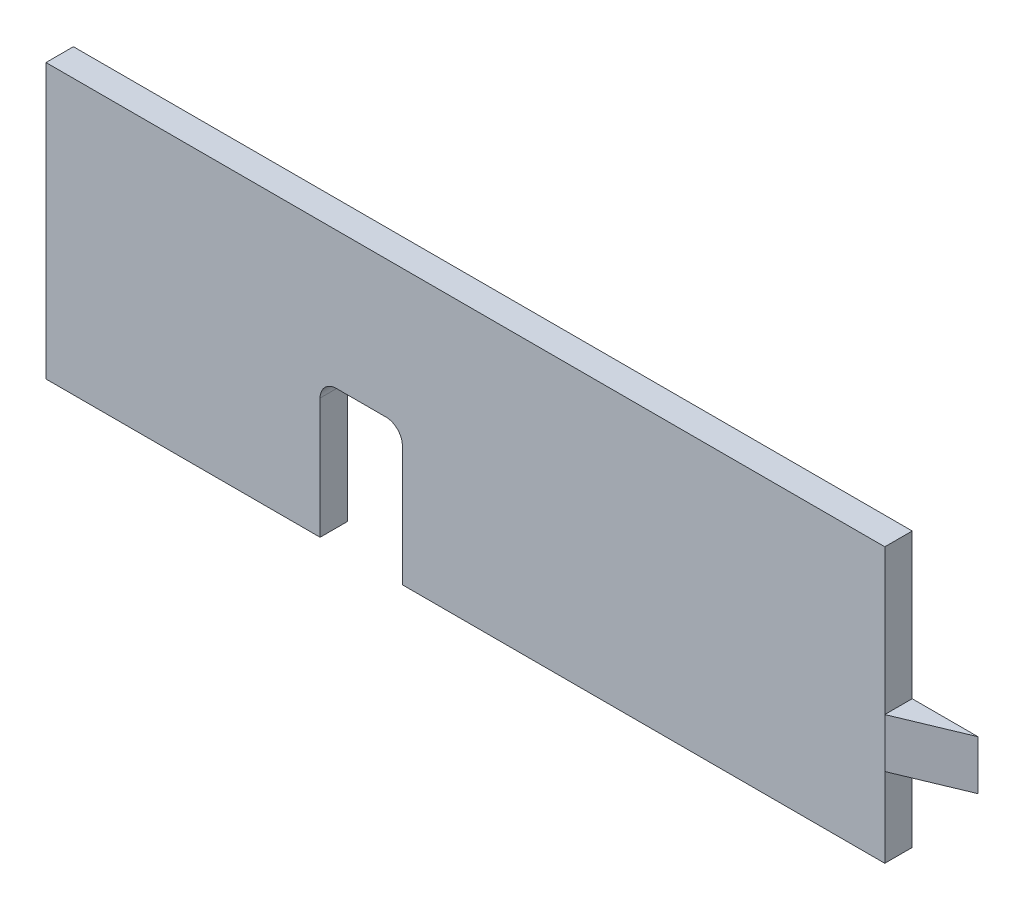
SolidWorks part; units mm, degrees
ref_plane "Front Plane" through (0, 0, 0) normal (0, 0, 1) x (1, 0, 0)
ref_plane "Top Plane" through (0, 0, 0) normal (0, 1, 0) x (1, 0, 0)
ref_plane "Right Plane" through (0, 0, 0) normal (1, 0, 0) x (0, 0, -1)
sketch "Sketch1" plane through (0, 0, 0) normal (0, 0, 1) x (1, 0, 0)
  line L1 (-76.5, -25) -> (76.5, -25)
  line L2 (-76.5, -25) -> (-76.5, 25)
  line L3 (-76.5, 25) -> (76.5, 25)
  line L4 (76.5, -25) -> (76.5, 25)
  line L5 (-76.5, -25) -> (76.5, 25) construction
  line L6 (-76.5, 25) -> (76.5, -25) construction
  point P0 (0, 0)
  dimension "D1" = 153
  dimension "D2" = 50
extrude "Boss-Extrude1" add sketch "Sketch1" along normal mid plane 5
sketch "Sketch2" plane through (0, 0, 2.5) normal (0, 0, 1) x (1, 0, 0)
  line L0 (-26.5, -25) -> (-26.5, -3)
  line L1 (-76.5, -25) -> (76.5, -25) construction
  line L2 (-23.5, 0) -> (-14.5, 0)
  line L3 (-11.5, -3) -> (-11.5, -25)
  line L4 (-76.5, 25) -> (-76.5, -25) construction
  line L5 (-26.5, -25) -> (-11.5, -25)
  arc A0 (-26.5, -3) -> (-23.5, 0) centre (-23.5, -3) cw
  arc A1 (-14.5, 0) -> (-11.5, -3) centre (-14.5, -3) cw
  dimension "D1" = 3
  dimension "D2" = 15
  dimension "D3" = 50
  dimension "D4" = 25
extrude "Cut-Extrude1" cut sketch "Sketch2" against normal through all
sketch "Sketch5" plane through (76.5, 0, 0) normal (1, 0, 0) x (0, 0, -1)
  line L0 (-2.5, -25) -> (-2.5, 25) construction
  line L1 (-2.5, -10.5) -> (2.5, -10.5)
  line L2 (-2.5, -10.5) -> (-2.5, -1.5)
  line L4 (2.5, -10.5) -> (2.5, -1.5)
  line L5 (2.5, -25) -> (2.5, 25) construction
  line L6 (-2.5, -25) -> (2.5, -25) construction
  line L7 (-2.5, -1.5) -> (2.5, -1.5)
  dimension "D1" = 14.5
  dimension "D2" = 9
extrude "Boss-Extrude2" add sketch "Sketch5" along normal blind 12
sketch "Sketch7" plane through (0, -10.5, 0) normal (0, -1, 0) x (1, 0, 0)
  line L0 (76.5, 2.5) -> (88.5, -2.5)
  line L4 (76.5, 2.5) -> (76.5, -2.5)
  line L5 (76.5, -2.5) -> (88.5, -2.5)
  line L6 (88.5, -2.5) -> (88.5, 2.5)
  line L7 (88.5, 2.5) -> (76.5, 2.5)
  line L10 (88.5, -2.5) -> (88.5, 2.5)
  line L11 (88.5, 2.5) -> (76.5, 2.5)
  dimension "D1" = 0
extrude "Cut-Extrude2" cut sketch "Sketch7" against normal up to surface (9 mm away) up to face at (82.5, -1.5, 0)
